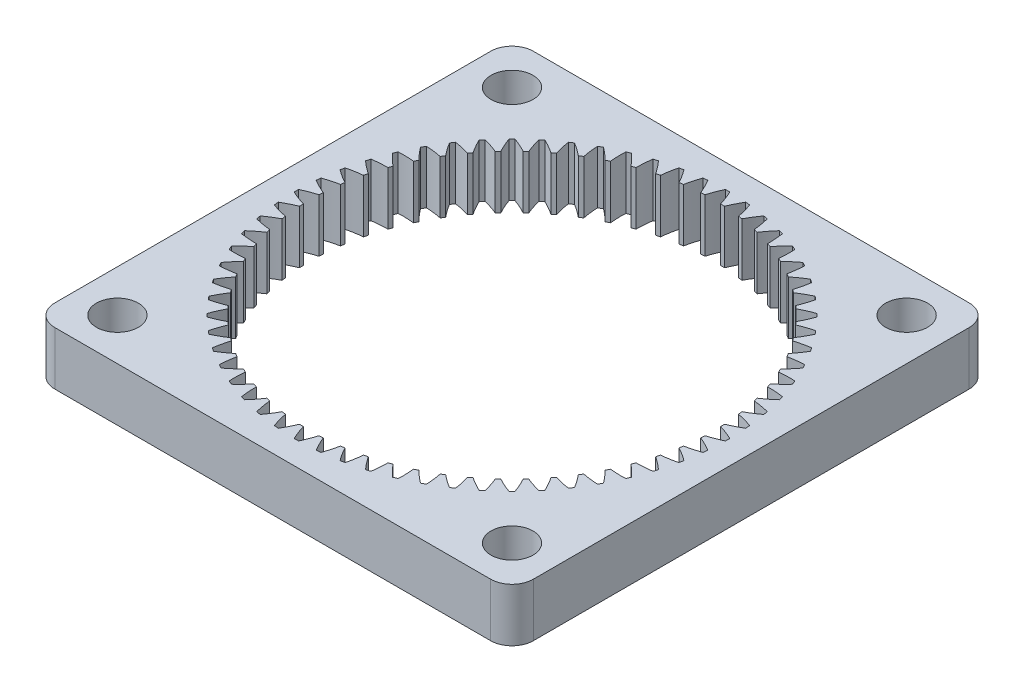
SolidWorks part; units mm, degrees
ref_plane "Front Plane" through (0, 0, 0) normal (0, 0, 1) x (1, 0, 0)
ref_plane "Top Plane" through (0, 0, 0) normal (0, 1, 0) x (1, 0, 0)
ref_plane "Right Plane" through (0, 0, 0) normal (1, 0, 0) x (0, 0, -1)
sketch "Sketch1" plane through (0, 0, 0) normal (0, 1, 0) x (1, 0, 0)
  line L0 (-119.0935, 26.7849) -> (-119.0935, 38.7516)
  line L1 (-64.6335, -15.7084) -> (-76.6002, -15.7084)
  line L2 (-62.0935, -13.1684) -> (-62.0935, -1.2017)
  line L3 (-64.6335, 41.2916) -> (-76.6002, 41.2916)
  line L4 (-119.0935, -13.1684) -> (-119.0935, -1.2017)
  line L5 (-62.0935, -15.7084) -> (-119.0935, 41.2916) construction
  line L6 (-62.0935, 41.2916) -> (-119.0935, -15.7084) construction
  line L7 (-104.5868, 41.2916) -> (-116.5535, 41.2916)
  line L8 (-62.0935, 26.7849) -> (-62.0935, 38.7516)
  line L9 (-104.5868, -15.7084) -> (-116.5535, -15.7084)
  line L10 (-119.0935, 26.7849) -> (-119.0935, -1.2017)
  line L11 (-104.5868, -15.7084) -> (-76.6002, -15.7084)
  line L12 (-62.0935, -1.2017) -> (-62.0935, 26.7849)
  line L13 (-76.6002, 41.2916) -> (-104.5868, 41.2916)
  arc A0 (-88.3348, 38.3748) -> (-89.182, 36.6846) centre (-77.7474, 32.0098) ccw
  arc A1 (-87.8179, 38.3239) -> (-88.3348, 38.3748) centre (-90.5935, 12.7916) ccw
  arc A2 (-87.3166, 36.5009) -> (-87.8179, 38.3239) centre (-99.4436, 34.1467) ccw
  arc A3 (-86.8469, 36.4312) -> (-87.3166, 36.5009) centre (-90.5935, 12.7916) ccw
  arc A4 (-85.8381, 38.0302) -> (-86.8469, 36.4312) centre (-75.9255, 30.6581) ccw
  arc A5 (-85.3286, 37.9288) -> (-85.8381, 38.0302) centre (-90.5935, 12.7916) ccw
  arc A6 (-85.0085, 36.0655) -> (-85.3286, 37.9288) centre (-97.3078, 34.9113) ccw
  arc A7 (-84.5479, 35.9502) -> (-85.0085, 36.0655) centre (-90.5935, 12.7916) ccw
  arc A8 (-83.3871, 37.4425) -> (-84.5479, 35.9502) centre (-74.2449, 29.1343) ccw
  arc A9 (-82.8901, 37.2918) -> (-83.3871, 37.4425) centre (-90.5935, 12.7916) ccw
  arc A10 (-82.7541, 35.406) -> (-82.8901, 37.2918) centre (-95.1074, 35.4629) ccw
  arc A11 (-82.307, 35.2461) -> (-82.7541, 35.406) centre (-90.5935, 12.7916) ccw
  arc A12 (-81.0056, 36.6175) -> (-82.307, 35.2461) centre (-72.7218, 27.4532) ccw
  arc A13 (-80.5258, 36.4187) -> (-81.0056, 36.6175) centre (-90.5935, 12.7916) ccw
  arc A14 (-80.5753, 34.5287) -> (-80.5258, 36.4187) centre (-92.8635, 35.7962) ccw
  arc A15 (-80.146, 34.3257) -> (-80.5753, 34.5287) centre (-90.5935, 12.7916) ccw
  arc A16 (-78.7165, 35.563) -> (-80.146, 34.3257) centre (-71.3707, 25.6309) ccw
  arc A17 (-78.2584, 35.3181) -> (-78.7165, 35.563) centre (-90.5935, 12.7916) ccw
  arc A18 (-78.4929, 33.4421) -> (-78.2584, 35.3181) centre (-90.5977, 35.9079) ccw
  arc A19 (-78.0856, 33.198) -> (-78.4929, 33.4421) centre (-90.5935, 12.7916) ccw
  arc A20 (-76.5417, 34.2892) -> (-78.0856, 33.198) centre (-70.2048, 23.6849) ccw
  arc A21 (-76.1098, 34.0006) -> (-76.5417, 34.2892) centre (-90.5935, 12.7916) ccw
  arc A22 (-76.527, 32.1566) -> (-76.1098, 34.0006) centre (-88.3319, 35.797) ccw
  arc A23 (-76.1457, 31.8737) -> (-76.527, 32.1566) centre (-90.5935, 12.7916) ccw
  arc A24 (-74.5022, 32.8083) -> (-76.1457, 31.8737) centre (-69.2353, 21.634) ccw
  arc A25 (-74.1007, 32.4788) -> (-74.5022, 32.8083) centre (-90.5935, 12.7916) ccw
  arc A26 (-74.6967, 30.6846) -> (-74.1007, 32.4788) centre (-86.0878, 35.4645) ccw
  arc A27 (-74.3449, 30.3657) -> (-74.6967, 30.6846) centre (-90.5935, 12.7916) ccw
  arc A28 (-72.6177, 31.1347) -> (-74.3449, 30.3657) centre (-68.4714, 19.4979) ccw
  arc A29 (-72.2504, 30.7674) -> (-72.6177, 31.1347) centre (-90.5935, 12.7916) ccw
  arc A30 (-73.0194, 29.0403) -> (-72.2504, 30.7674) centre (-83.8872, 34.9137) ccw
  arc A31 (-72.7005, 28.6885) -> (-73.0194, 29.0403) centre (-90.5935, 12.7916) ccw
  arc A32 (-70.9063, 29.2844) -> (-72.7005, 28.6885) centre (-67.9206, 17.2973) ccw
  arc A33 (-70.5768, 28.8829) -> (-70.9063, 29.2844) centre (-90.5935, 12.7916) ccw
  arc A34 (-71.5114, 27.2395) -> (-70.5768, 28.8829) centre (-81.7511, 34.1498) ccw
  arc A35 (-71.2285, 26.8581) -> (-71.5114, 27.2395) centre (-90.5935, 12.7916) ccw
  arc A36 (-69.3845, 27.2753) -> (-71.2285, 26.8581) centre (-67.5882, 15.0533) ccw
  arc A37 (-69.096, 26.8435) -> (-69.3845, 27.2753) centre (-90.5935, 12.7916) ccw
  arc A38 (-70.1871, 25.2995) -> (-69.096, 26.8435) centre (-79.7003, 33.1803) ccw
  arc A39 (-69.943, 24.8922) -> (-70.1871, 25.2995) centre (-90.5935, 12.7916) ccw
  arc A40 (-68.067, 25.1268) -> (-69.943, 24.8922) centre (-67.4773, 12.7874) ccw
  arc A41 (-67.8222, 24.6687) -> (-68.067, 25.1268) centre (-90.5935, 12.7916) ccw
  arc A42 (-69.0594, 23.2391) -> (-67.8222, 24.6687) centre (-77.7543, 32.0144) ccw
  arc A43 (-68.8564, 22.8099) -> (-69.0594, 23.2391) centre (-90.5935, 12.7916) ccw
  arc A44 (-66.9664, 22.8594) -> (-68.8564, 22.8099) centre (-67.589, 10.5217) ccw
  arc A45 (-66.7676, 22.3795) -> (-66.9664, 22.8594) centre (-90.5935, 12.7916) ccw
  arc A46 (-68.1391, 21.0781) -> (-66.7676, 22.3795) centre (-75.9319, 30.6634) ccw
  arc A47 (-67.9791, 20.631) -> (-68.1391, 21.0781) centre (-90.5935, 12.7916) ccw
  arc A48 (-66.0934, 20.495) -> (-67.9791, 20.631) centre (-67.9222, 8.2778) ccw
  arc A49 (-65.9426, 19.998) -> (-66.0934, 20.495) centre (-90.5935, 12.7916) ccw
  arc A50 (-67.435, 18.8373) -> (-65.9426, 19.998) centre (-74.2508, 29.1402) ccw
  arc A51 (-67.3196, 18.3767) -> (-67.435, 18.8373) centre (-90.5935, 12.7916) ccw
  arc A52 (-65.4563, 18.0565) -> (-67.3196, 18.3767) centre (-68.4738, 6.0773) ccw
  arc A53 (-65.3549, 17.5471) -> (-65.4563, 18.0565) centre (-90.5935, 12.7916) ccw
  arc A54 (-66.9539, 16.5382) -> (-65.3549, 17.5471) centre (-72.727, 27.4596) ccw
  arc A55 (-66.8842, 16.0685) -> (-66.9539, 16.5382) centre (-90.5935, 12.7916) ccw
  arc A56 (-65.0613, 15.5673) -> (-66.8842, 16.0685) centre (-69.2385, 3.9415) ccw
  arc A57 (-65.0104, 15.0504) -> (-65.0613, 15.5673) centre (-90.5935, 12.7916) ccw
  arc A58 (-66.7005, 14.2031) -> (-65.0104, 15.0504) centre (-71.3754, 25.6378) ccw
  arc A59 (-66.6772, 13.7288) -> (-66.7005, 14.2031) centre (-90.5935, 12.7916) ccw
  arc A60 (-64.9122, 13.0513) -> (-66.6772, 13.7288) centre (-70.2087, 1.891) ccw
  arc A61 (-64.9122, 12.5319) -> (-64.9122, 13.0513) centre (-90.5935, 12.7916) ccw
  arc A62 (-66.6772, 11.8544) -> (-64.9122, 12.5319) centre (-70.2087, 23.6922) ccw
  arc A63 (-66.7005, 11.3801) -> (-66.6772, 11.8544) centre (-90.5935, 12.7916) ccw
  arc A64 (-65.0104, 10.5328) -> (-66.7005, 11.3801) centre (-71.3754, -0.0546) ccw
  arc A65 (-65.0613, 10.0159) -> (-65.0104, 10.5328) centre (-90.5935, 12.7916) ccw
  arc A66 (-66.8842, 9.5147) -> (-65.0613, 10.0159) centre (-69.2385, 21.6416) ccw
  arc A67 (-66.9539, 9.045) -> (-66.8842, 9.5147) centre (-90.5935, 12.7916) ccw
  arc A68 (-65.3549, 8.0361) -> (-66.9539, 9.045) centre (-72.727, -1.8764) ccw
  arc A69 (-65.4563, 7.5267) -> (-65.3549, 8.0361) centre (-90.5935, 12.7916) ccw
  arc A70 (-67.3196, 7.2065) -> (-65.4563, 7.5267) centre (-68.4738, 19.5059) ccw
  arc A71 (-67.435, 6.7459) -> (-67.3196, 7.2065) centre (-90.5935, 12.7916) ccw
  arc A72 (-65.9426, 5.5852) -> (-67.435, 6.7459) centre (-74.2508, -3.557) ccw
  arc A73 (-66.0934, 5.0882) -> (-65.9426, 5.5852) centre (-90.5935, 12.7916) ccw
  arc A74 (-67.9791, 4.9522) -> (-66.0934, 5.0882) centre (-67.9222, 17.3054) ccw
  arc A75 (-68.1391, 4.5051) -> (-67.9791, 4.9522) centre (-90.5935, 12.7916) ccw
  arc A76 (-66.7676, 3.2037) -> (-68.1391, 4.5051) centre (-75.9319, -5.0802) ccw
  arc A77 (-66.9664, 2.7238) -> (-66.7676, 3.2037) centre (-90.5935, 12.7916) ccw
  arc A78 (-68.8564, 2.7733) -> (-66.9664, 2.7238) centre (-67.589, 15.0615) ccw
  arc A79 (-69.0594, 2.3441) -> (-68.8564, 2.7733) centre (-90.5935, 12.7916) ccw
  arc A80 (-67.8222, 0.9145) -> (-69.0594, 2.3441) centre (-77.7543, -6.4312) ccw
  arc A81 (-68.067, 0.4564) -> (-67.8222, 0.9145) centre (-90.5935, 12.7916) ccw
  arc A82 (-69.943, 0.6909) -> (-68.067, 0.4564) centre (-67.4773, 12.7957) ccw
  arc A83 (-70.1871, 0.2837) -> (-69.943, 0.6909) centre (-90.5935, 12.7916) ccw
  arc A84 (-69.096, -1.2603) -> (-70.1871, 0.2837) centre (-79.7003, -7.5971) ccw
  arc A85 (-69.3845, -1.6921) -> (-69.096, -1.2603) centre (-90.5935, 12.7916) ccw
  arc A86 (-71.2285, -1.2749) -> (-69.3845, -1.6921) centre (-67.5882, 10.5299) ccw
  arc A87 (-71.5114, -1.6563) -> (-71.2285, -1.2749) centre (-90.5935, 12.7916) ccw
  arc A88 (-70.5768, -3.2997) -> (-71.5114, -1.6563) centre (-81.7511, -8.5666) ccw
  arc A89 (-70.9063, -3.7013) -> (-70.5768, -3.2997) centre (-90.5935, 12.7916) ccw
  arc A90 (-72.7005, -3.1053) -> (-70.9063, -3.7013) centre (-67.9206, 8.2859) ccw
  arc A91 (-73.0194, -3.4571) -> (-72.7005, -3.1053) centre (-90.5935, 12.7916) ccw
  arc A92 (-72.2504, -5.1842) -> (-73.0194, -3.4571) centre (-83.8872, -9.3305) ccw
  arc A93 (-72.6177, -5.5515) -> (-72.2504, -5.1842) centre (-90.5935, 12.7916) ccw
  arc A94 (-74.3449, -4.7825) -> (-72.6177, -5.5515) centre (-68.4714, 6.0853) ccw
  arc A95 (-74.6967, -5.1014) -> (-74.3449, -4.7825) centre (-90.5935, 12.7916) ccw
  arc A96 (-74.1007, -6.8956) -> (-74.6967, -5.1014) centre (-86.0878, -9.8813) ccw
  arc A97 (-74.5022, -7.2251) -> (-74.1007, -6.8956) centre (-90.5935, 12.7916) ccw
  arc A98 (-76.1457, -6.2906) -> (-74.5022, -7.2251) centre (-69.2353, 3.9492) ccw
  arc A99 (-76.527, -6.5734) -> (-76.1457, -6.2906) centre (-90.5935, 12.7916) ccw
  arc A100 (-76.1098, -8.4174) -> (-76.527, -6.5734) centre (-88.3319, -10.2138) ccw
  arc A101 (-76.5417, -8.706) -> (-76.1098, -8.4174) centre (-90.5935, 12.7916) ccw
  arc A102 (-78.0856, -7.6148) -> (-76.5417, -8.706) centre (-70.2048, 1.8983) ccw
  arc A103 (-78.4929, -7.8589) -> (-78.0856, -7.6148) centre (-90.5935, 12.7916) ccw
  arc A104 (-78.2584, -9.7349) -> (-78.4929, -7.8589) centre (-90.5977, -10.3247) ccw
  arc A105 (-78.7165, -9.9798) -> (-78.2584, -9.7349) centre (-90.5935, 12.7916) ccw
  arc A106 (-80.146, -8.7425) -> (-78.7165, -9.9798) centre (-71.3707, -0.0477) ccw
  arc A107 (-80.5753, -8.9455) -> (-80.146, -8.7425) centre (-90.5935, 12.7916) ccw
  arc A108 (-80.5258, -10.8355) -> (-80.5753, -8.9455) centre (-92.8635, -10.213) ccw
  arc A109 (-81.0056, -11.0343) -> (-80.5258, -10.8355) centre (-90.5935, 12.7916) ccw
  arc A110 (-82.307, -9.6629) -> (-81.0056, -11.0343) centre (-72.7218, -1.87) ccw
  arc A111 (-82.7541, -9.8228) -> (-82.307, -9.6629) centre (-90.5935, 12.7916) ccw
  arc A112 (-82.8901, -11.7086) -> (-82.7541, -9.8228) centre (-95.1074, -9.8797) ccw
  arc A113 (-83.3871, -11.8593) -> (-82.8901, -11.7086) centre (-90.5935, 12.7916) ccw
  arc A114 (-84.5479, -10.367) -> (-83.3871, -11.8593) centre (-74.2449, -3.5511) ccw
  arc A115 (-85.0085, -10.4823) -> (-84.5479, -10.367) centre (-90.5935, 12.7916) ccw
  arc A116 (-85.3286, -12.3457) -> (-85.0085, -10.4823) centre (-97.3078, -9.3281) ccw
  arc A117 (-85.8381, -12.447) -> (-85.3286, -12.3457) centre (-90.5935, 12.7916) ccw
  arc A118 (-86.8469, -10.848) -> (-85.8381, -12.447) centre (-75.9255, -5.0749) ccw
  arc A119 (-87.3166, -10.9177) -> (-86.8469, -10.848) centre (-90.5935, 12.7916) ccw
  arc A120 (-87.8179, -12.7407) -> (-87.3166, -10.9177) centre (-99.4436, -8.5635) ccw
  arc A121 (-88.3348, -12.7916) -> (-87.8179, -12.7407) centre (-90.5935, 12.7916) ccw
  arc A122 (-89.182, -11.1014) -> (-88.3348, -12.7916) centre (-77.7474, -6.4266) ccw
  arc A123 (-89.6563, -11.1247) -> (-89.182, -11.1014) centre (-90.5935, 12.7916) ccw
  arc A124 (-90.3338, -12.8898) -> (-89.6563, -11.1247) centre (-101.4941, -7.5932) ccw
  arc A125 (-90.8532, -12.8898) -> (-90.3338, -12.8898) centre (-90.5935, 12.7916) ccw
  arc A126 (-91.5308, -11.1247) -> (-90.8532, -12.8898) centre (-79.6929, -7.5932) ccw
  arc A127 (-92.005, -11.1014) -> (-91.5308, -11.1247) centre (-90.5935, 12.7916) ccw
  arc A128 (-92.8523, -12.7916) -> (-92.005, -11.1014) centre (-103.4397, -6.4266) ccw
  arc A129 (-93.3692, -12.7407) -> (-92.8523, -12.7916) centre (-90.5935, 12.7916) ccw
  arc A130 (-93.8705, -10.9177) -> (-93.3692, -12.7407) centre (-81.7435, -8.5635) ccw
  arc A131 (-94.3401, -10.848) -> (-93.8705, -10.9177) centre (-90.5935, 12.7916) ccw
  arc A132 (-95.349, -12.447) -> (-94.3401, -10.848) centre (-105.2616, -5.0749) ccw
  arc A133 (-95.8584, -12.3457) -> (-95.349, -12.447) centre (-90.5935, 12.7916) ccw
  arc A134 (-96.1786, -10.4823) -> (-95.8584, -12.3457) centre (-83.8793, -9.3281) ccw
  arc A135 (-96.6392, -10.367) -> (-96.1786, -10.4823) centre (-90.5935, 12.7916) ccw
  arc A136 (-97.7999, -11.8593) -> (-96.6392, -10.367) centre (-106.9421, -3.5511) ccw
  arc A137 (-98.297, -11.7086) -> (-97.7999, -11.8593) centre (-90.5935, 12.7916) ccw
  arc A138 (-98.433, -9.8228) -> (-98.297, -11.7086) centre (-86.0797, -9.8797) ccw
  arc A139 (-98.88, -9.6629) -> (-98.433, -9.8228) centre (-90.5935, 12.7916) ccw
  arc A140 (-100.1814, -11.0343) -> (-98.88, -9.6629) centre (-108.4653, -1.87) ccw
  arc A141 (-100.6613, -10.8355) -> (-100.1814, -11.0343) centre (-90.5935, 12.7916) ccw
  arc A142 (-100.6118, -8.9455) -> (-100.6613, -10.8355) centre (-88.3236, -10.213) ccw
  arc A143 (-101.041, -8.7425) -> (-100.6118, -8.9455) centre (-90.5935, 12.7916) ccw
  arc A144 (-102.4706, -9.9798) -> (-101.041, -8.7425) centre (-109.8163, -0.0477) ccw
  arc A145 (-102.9287, -9.7349) -> (-102.4706, -9.9798) centre (-90.5935, 12.7916) ccw
  arc A146 (-102.6942, -7.8589) -> (-102.9287, -9.7349) centre (-90.5894, -10.3247) ccw
  arc A147 (-103.1014, -7.6148) -> (-102.6942, -7.8589) centre (-90.5935, 12.7916) ccw
  arc A148 (-104.6454, -8.706) -> (-103.1014, -7.6148) centre (-110.9822, 1.8983) ccw
  arc A149 (-105.0773, -8.4174) -> (-104.6454, -8.706) centre (-90.5935, 12.7916) ccw
  arc A150 (-104.66, -6.5734) -> (-105.0773, -8.4174) centre (-92.8552, -10.2138) ccw
  arc A151 (-105.0414, -6.2906) -> (-104.66, -6.5734) centre (-90.5935, 12.7916) ccw
  arc A152 (-106.6849, -7.2251) -> (-105.0414, -6.2906) centre (-111.9518, 3.9492) ccw
  arc A153 (-107.0864, -6.8956) -> (-106.6849, -7.2251) centre (-90.5935, 12.7916) ccw
  arc A154 (-106.4904, -5.1014) -> (-107.0864, -6.8956) centre (-95.0992, -9.8813) ccw
  arc A155 (-106.8422, -4.7825) -> (-106.4904, -5.1014) centre (-90.5935, 12.7916) ccw
  arc A156 (-108.5694, -5.5515) -> (-106.8422, -4.7825) centre (-112.7156, 6.0853) ccw
  arc A157 (-108.9366, -5.1842) -> (-108.5694, -5.5515) centre (-90.5935, 12.7916) ccw
  arc A158 (-108.1677, -3.4571) -> (-108.9366, -5.1842) centre (-97.2999, -9.3305) ccw
  arc A159 (-108.4865, -3.1053) -> (-108.1677, -3.4571) centre (-90.5935, 12.7916) ccw
  arc A160 (-110.2808, -3.7013) -> (-108.4865, -3.1053) centre (-113.2664, 8.2859) ccw
  arc A161 (-110.6103, -3.2997) -> (-110.2808, -3.7013) centre (-90.5935, 12.7916) ccw
  arc A162 (-109.6757, -1.6563) -> (-110.6103, -3.2997) centre (-99.4359, -8.5666) ccw
  arc A163 (-109.9585, -1.2749) -> (-109.6757, -1.6563) centre (-90.5935, 12.7916) ccw
  arc A164 (-111.8025, -1.6921) -> (-109.9585, -1.2749) centre (-113.5989, 10.5299) ccw
  arc A165 (-112.0911, -1.2603) -> (-111.8025, -1.6921) centre (-90.5935, 12.7916) ccw
  arc A166 (-110.9999, 0.2837) -> (-112.0911, -1.2603) centre (-101.4868, -7.5971) ccw
  arc A167 (-111.244, 0.6909) -> (-110.9999, 0.2837) centre (-90.5935, 12.7916) ccw
  arc A168 (-113.1201, 0.4564) -> (-111.244, 0.6909) centre (-113.7098, 12.7957) ccw
  arc A169 (-113.3649, 0.9145) -> (-113.1201, 0.4564) centre (-90.5935, 12.7916) ccw
  arc A170 (-112.1277, 2.3441) -> (-113.3649, 0.9145) centre (-103.4328, -6.4312) ccw
  arc A171 (-112.3307, 2.7733) -> (-112.1277, 2.3441) centre (-90.5935, 12.7916) ccw
  arc A172 (-114.2207, 2.7238) -> (-112.3307, 2.7733) centre (-113.5981, 15.0615) ccw
  arc A173 (-114.4194, 3.2037) -> (-114.2207, 2.7238) centre (-90.5935, 12.7916) ccw
  arc A174 (-113.048, 4.5051) -> (-114.4194, 3.2037) centre (-105.2551, -5.0802) ccw
  arc A175 (-113.208, 4.9522) -> (-113.048, 4.5051) centre (-90.5935, 12.7916) ccw
  arc A176 (-115.0937, 5.0882) -> (-113.208, 4.9522) centre (-113.2648, 17.3054) ccw
  arc A177 (-115.2445, 5.5852) -> (-115.0937, 5.0882) centre (-90.5935, 12.7916) ccw
  arc A178 (-113.7521, 6.7459) -> (-115.2445, 5.5852) centre (-106.9363, -3.557) ccw
  arc A179 (-113.8675, 7.2065) -> (-113.7521, 6.7459) centre (-90.5935, 12.7916) ccw
  arc A180 (-115.7308, 7.5267) -> (-113.8675, 7.2065) centre (-112.7132, 19.5059) ccw
  arc A181 (-115.8321, 8.0361) -> (-115.7308, 7.5267) centre (-90.5935, 12.7916) ccw
  arc A182 (-114.2332, 9.045) -> (-115.8321, 8.0361) centre (-108.46, -1.8764) ccw
  arc A183 (-114.3028, 9.5147) -> (-114.2332, 9.045) centre (-90.5935, 12.7916) ccw
  arc A184 (-116.1258, 10.0159) -> (-114.3028, 9.5147) centre (-111.9486, 21.6416) ccw
  arc A185 (-116.1767, 10.5328) -> (-116.1258, 10.0159) centre (-90.5935, 12.7916) ccw
  arc A186 (-114.4866, 11.3801) -> (-116.1767, 10.5328) centre (-109.8117, -0.0546) ccw
  arc A187 (-114.5099, 11.8544) -> (-114.4866, 11.3801) centre (-90.5935, 12.7916) ccw
  arc A188 (-116.2749, 12.5319) -> (-114.5099, 11.8544) centre (-110.9783, 23.6922) ccw
  arc A189 (-116.2749, 13.0513) -> (-116.2749, 12.5319) centre (-90.5935, 12.7916) ccw
  arc A190 (-114.5099, 13.7288) -> (-116.2749, 13.0513) centre (-110.9783, 1.891) ccw
  arc A191 (-114.4866, 14.2031) -> (-114.5099, 13.7288) centre (-90.5935, 12.7916) ccw
  arc A192 (-116.1767, 15.0504) -> (-114.4866, 14.2031) centre (-109.8117, 25.6378) ccw
  arc A193 (-116.1258, 15.5673) -> (-116.1767, 15.0504) centre (-90.5935, 12.7916) ccw
  arc A194 (-114.3028, 16.0685) -> (-116.1258, 15.5673) centre (-111.9486, 3.9415) ccw
  arc A195 (-114.2332, 16.5382) -> (-114.3028, 16.0685) centre (-90.5935, 12.7916) ccw
  arc A196 (-115.8321, 17.5471) -> (-114.2332, 16.5382) centre (-108.46, 27.4596) ccw
  arc A197 (-115.7308, 18.0565) -> (-115.8321, 17.5471) centre (-90.5935, 12.7916) ccw
  arc A198 (-113.8675, 18.3767) -> (-115.7308, 18.0565) centre (-112.7132, 6.0773) ccw
  arc A199 (-113.7521, 18.8373) -> (-113.8675, 18.3767) centre (-90.5935, 12.7916) ccw
  arc A200 (-115.2445, 19.998) -> (-113.7521, 18.8373) centre (-106.9363, 29.1402) ccw
  arc A201 (-115.0937, 20.495) -> (-115.2445, 19.998) centre (-90.5935, 12.7916) ccw
  arc A202 (-113.208, 20.631) -> (-115.0937, 20.495) centre (-113.2648, 8.2778) ccw
  arc A203 (-113.048, 21.0781) -> (-113.208, 20.631) centre (-90.5935, 12.7916) ccw
  arc A204 (-114.4194, 22.3795) -> (-113.048, 21.0781) centre (-105.2551, 30.6634) ccw
  arc A205 (-114.2207, 22.8594) -> (-114.4194, 22.3795) centre (-90.5935, 12.7916) ccw
  arc A206 (-112.3307, 22.8099) -> (-114.2207, 22.8594) centre (-113.5981, 10.5217) ccw
  arc A207 (-112.1277, 23.2391) -> (-112.3307, 22.8099) centre (-90.5935, 12.7916) ccw
  arc A208 (-113.3649, 24.6687) -> (-112.1277, 23.2391) centre (-103.4328, 32.0144) ccw
  arc A209 (-113.1201, 25.1268) -> (-113.3649, 24.6687) centre (-90.5935, 12.7916) ccw
  arc A210 (-111.244, 24.8922) -> (-113.1201, 25.1268) centre (-113.7098, 12.7874) ccw
  arc A211 (-110.9999, 25.2995) -> (-111.244, 24.8922) centre (-90.5935, 12.7916) ccw
  arc A212 (-112.0911, 26.8435) -> (-110.9999, 25.2995) centre (-101.4868, 33.1803) ccw
  arc A213 (-111.8025, 27.2753) -> (-112.0911, 26.8435) centre (-90.5935, 12.7916) ccw
  arc A214 (-109.9585, 26.8581) -> (-111.8025, 27.2753) centre (-113.5989, 15.0533) ccw
  arc A215 (-109.6757, 27.2395) -> (-109.9585, 26.8581) centre (-90.5935, 12.7916) ccw
  arc A216 (-110.6103, 28.8829) -> (-109.6757, 27.2395) centre (-99.4359, 34.1498) ccw
  arc A217 (-110.2808, 29.2844) -> (-110.6103, 28.8829) centre (-90.5935, 12.7916) ccw
  arc A218 (-108.4865, 28.6885) -> (-110.2808, 29.2844) centre (-113.2664, 17.2973) ccw
  arc A219 (-108.1677, 29.0403) -> (-108.4865, 28.6885) centre (-90.5935, 12.7916) ccw
  arc A220 (-108.9366, 30.7674) -> (-108.1677, 29.0403) centre (-97.2999, 34.9137) ccw
  arc A221 (-108.5694, 31.1347) -> (-108.9366, 30.7674) centre (-90.5935, 12.7916) ccw
  arc A222 (-106.8422, 30.3657) -> (-108.5694, 31.1347) centre (-112.7156, 19.4979) ccw
  arc A223 (-106.4904, 30.6846) -> (-106.8422, 30.3657) centre (-90.5935, 12.7916) ccw
  arc A224 (-107.0864, 32.4788) -> (-106.4904, 30.6846) centre (-95.0992, 35.4645) ccw
  arc A225 (-106.6849, 32.8083) -> (-107.0864, 32.4788) centre (-90.5935, 12.7916) ccw
  arc A226 (-105.0414, 31.8737) -> (-106.6849, 32.8083) centre (-111.9518, 21.634) ccw
  arc A227 (-104.66, 32.1566) -> (-105.0414, 31.8737) centre (-90.5935, 12.7916) ccw
  arc A228 (-105.0773, 34.0006) -> (-104.66, 32.1566) centre (-92.8552, 35.797) ccw
  arc A229 (-104.6454, 34.2892) -> (-105.0773, 34.0006) centre (-90.5935, 12.7916) ccw
  arc A230 (-103.1014, 33.198) -> (-104.6454, 34.2892) centre (-110.9822, 23.6849) ccw
  arc A231 (-102.6942, 33.4421) -> (-103.1014, 33.198) centre (-90.5935, 12.7916) ccw
  arc A232 (-102.9287, 35.3181) -> (-102.6942, 33.4421) centre (-90.5894, 35.9079) ccw
  arc A233 (-102.4706, 35.563) -> (-102.9287, 35.3181) centre (-90.5935, 12.7916) ccw
  arc A234 (-101.041, 34.3257) -> (-102.4706, 35.563) centre (-109.8163, 25.6309) ccw
  arc A235 (-100.6118, 34.5287) -> (-101.041, 34.3257) centre (-90.5935, 12.7916) ccw
  arc A236 (-100.6613, 36.4187) -> (-100.6118, 34.5287) centre (-88.3236, 35.7962) ccw
  arc A237 (-100.1814, 36.6175) -> (-100.6613, 36.4187) centre (-90.5935, 12.7916) ccw
  arc A238 (-98.88, 35.2461) -> (-100.1814, 36.6175) centre (-108.4653, 27.4532) ccw
  arc A239 (-98.433, 35.406) -> (-98.88, 35.2461) centre (-90.5935, 12.7916) ccw
  arc A240 (-98.297, 37.2918) -> (-98.433, 35.406) centre (-86.0797, 35.4629) ccw
  arc A241 (-97.7999, 37.4425) -> (-98.297, 37.2918) centre (-90.5935, 12.7916) ccw
  arc A242 (-96.6392, 35.9502) -> (-97.7999, 37.4425) centre (-106.9421, 29.1343) ccw
  arc A243 (-96.1786, 36.0655) -> (-96.6392, 35.9502) centre (-90.5935, 12.7916) ccw
  arc A244 (-95.8584, 37.9288) -> (-96.1786, 36.0655) centre (-83.8793, 34.9113) ccw
  arc A245 (-95.349, 38.0302) -> (-95.8584, 37.9288) centre (-90.5935, 12.7916) ccw
  arc A246 (-94.3401, 36.4312) -> (-95.349, 38.0302) centre (-105.2616, 30.6581) ccw
  arc A247 (-93.8705, 36.5009) -> (-94.3401, 36.4312) centre (-90.5935, 12.7916) ccw
  arc A248 (-93.3692, 38.3239) -> (-93.8705, 36.5009) centre (-81.7435, 34.1467) ccw
  arc A249 (-92.8523, 38.3748) -> (-93.3692, 38.3239) centre (-90.5935, 12.7916) ccw
  arc A250 (-92.005, 36.6846) -> (-92.8523, 38.3748) centre (-103.4397, 32.0098) ccw
  arc A251 (-91.5308, 36.7079) -> (-92.005, 36.6846) centre (-90.5935, 12.7916) ccw
  arc A252 (-90.8532, 38.473) -> (-91.5308, 36.7079) centre (-79.6929, 33.1764) ccw
  arc A253 (-90.3338, 38.473) -> (-90.8532, 38.473) centre (-90.5935, 12.7916) ccw
  arc A254 (-89.6563, 36.7079) -> (-90.3338, 38.473) centre (-101.4941, 33.1764) ccw
  arc A255 (-89.182, 36.6846) -> (-89.6563, 36.7079) centre (-90.5935, 12.7916) ccw
  arc A260 (-116.5535, -15.7084) -> (-119.0935, -13.1684) centre (-116.5535, -13.1684) cw
  arc A261 (-64.6335, -15.7084) -> (-62.0935, -13.1684) centre (-64.6335, -13.1684) ccw
  arc A262 (-62.0935, 38.7516) -> (-64.6335, 41.2916) centre (-64.6335, 38.7516) ccw
  arc A263 (-116.5535, 41.2916) -> (-119.0935, 38.7516) centre (-116.5535, 38.7516) ccw
  circle A264 centre (-114.0935, 36.2916) radius 2.5
  circle A265 centre (-67.0935, 36.2916) radius 2.5
  circle A266 centre (-67.0935, -10.7084) radius 2.5
  circle A267 centre (-114.0935, -10.7084) radius 2.5
  point P547 (-90.5935, 12.7916)
  dimension "D4" = 2.54
  dimension "D5" = 5
  dimension "D2" = 57
  dimension "D3" = 57
  dimension "D6" = 5
  dimension "D7" = 4
extrude "Boss-Extrude1" add sketch "Sketch1" along normal blind 6.35
